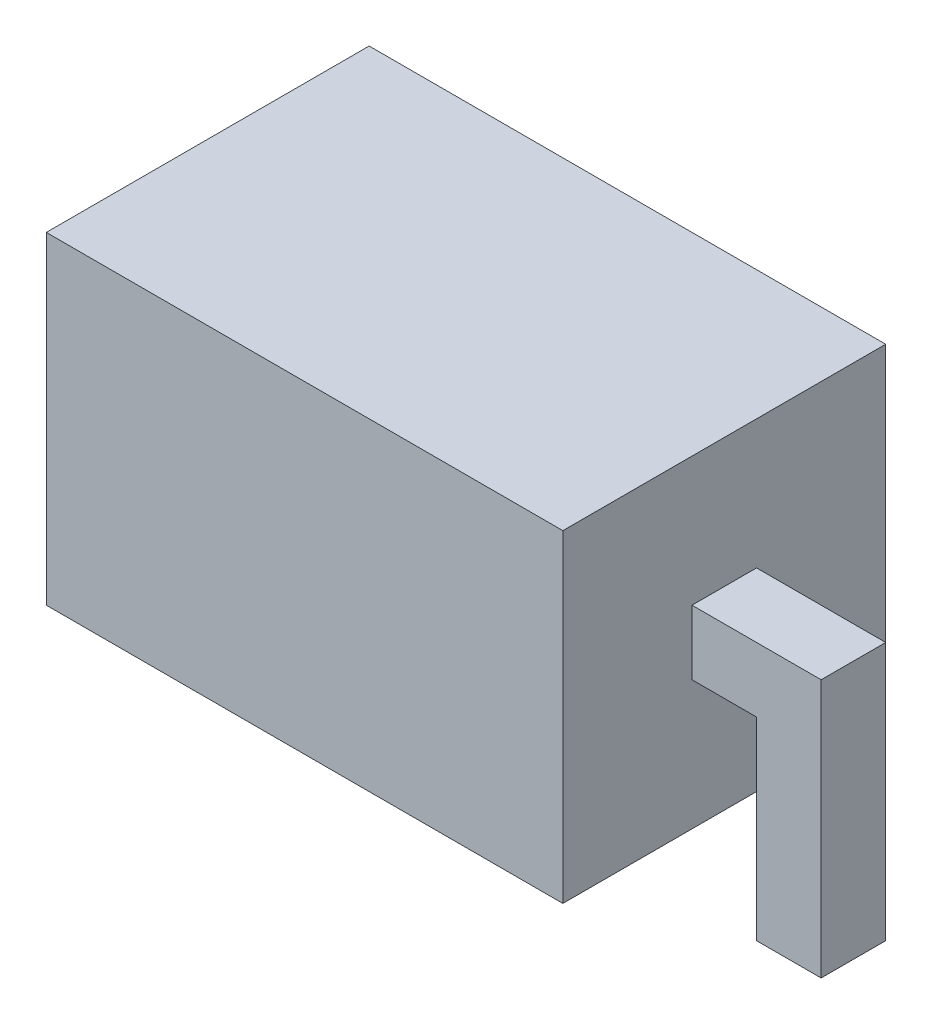
SolidWorks part; units mm, degrees
ref_plane "Front Plane" through (0, 0, 0) normal (0, 0, 1) x (1, 0, 0)
ref_plane "Top Plane" through (0, 0, 0) normal (0, 1, 0) x (1, 0, 0)
ref_plane "Right Plane" through (0, 0, 0) normal (1, 0, 0) x (0, 0, -1)
sketch "Sketch99" plane through (0, 0, 0) normal (0, 0, 1) x (1, 0, 0)
  line L1 (-2, -1.25) -> (2, -1.25)
  line L2 (-2, -1.25) -> (-2, 1.25)
  line L3 (-2, 1.25) -> (2, 1.25)
  line L4 (2, -1.25) -> (2, 1.25)
  line L5 (-2, -1.25) -> (2, 1.25) construction
  line L6 (-2, 1.25) -> (2, -1.25) construction
  point P0 (0, 0)
  dimension "D1" = 4
  dimension "D2" = 2.5
extrude "Boss-Extrude5" add sketch "Sketch99" along normal blind 2.5
ref_plane "Plane3" through (0, 0, 1.25) normal (0, 0, 1) x (1, 0, 0)
sketch "Sketch100" plane through (0, 0, 1.25) normal (0, 0, 1) x (1, 0, 0)
  line L0 (2, -0.25) -> (2, 0.25)
  line L1 (2, -1.25) -> (2, 1.25) construction
  line L2 (2, 0.25) -> (3, 0.25)
  line L3 (3, 0.25) -> (3, -0.25)
  line L4 (2.5, -0.25) -> (2, -0.25)
  line L5 (2.5, -0.25) -> (2.5, -1.75)
  line L6 (2.5, -1.75) -> (3, -1.75)
  line L7 (3, -1.75) -> (3, 0.25)
  line L8 (0, 1.25) -> (0, -1.25) construction
  line L9 (2, 1.25) -> (-2, 1.25) construction
  line L10 (-2, -1.25) -> (2, -1.25) construction
  line L11 (-2.5, -1.75) -> (-3, -1.75)
  line L12 (-3, -1.75) -> (-3, 0.25)
  line L13 (-2.5, -0.25) -> (-2.5, -1.75)
  line L14 (-3, 0.25) -> (-3, -0.25)
  line L15 (-2, 0.25) -> (-3, 0.25)
  line L16 (-2, -0.25) -> (-2, 0.25)
  line L17 (-2.5, -0.25) -> (-2, -0.25)
  point P5 (2, 0)
  dimension "D1" = 0.5
  dimension "D2" = 1
  dimension "D3" = 0.5
  dimension "D4" = 2
extrude "Boss-Extrude6" add sketch "Sketch100" along normal blind 0.25 and the other way blind 0.25 contours L6 L7 L3 L2 L0 L4 L5 | L13 L17 L16 L15 L12 L11
